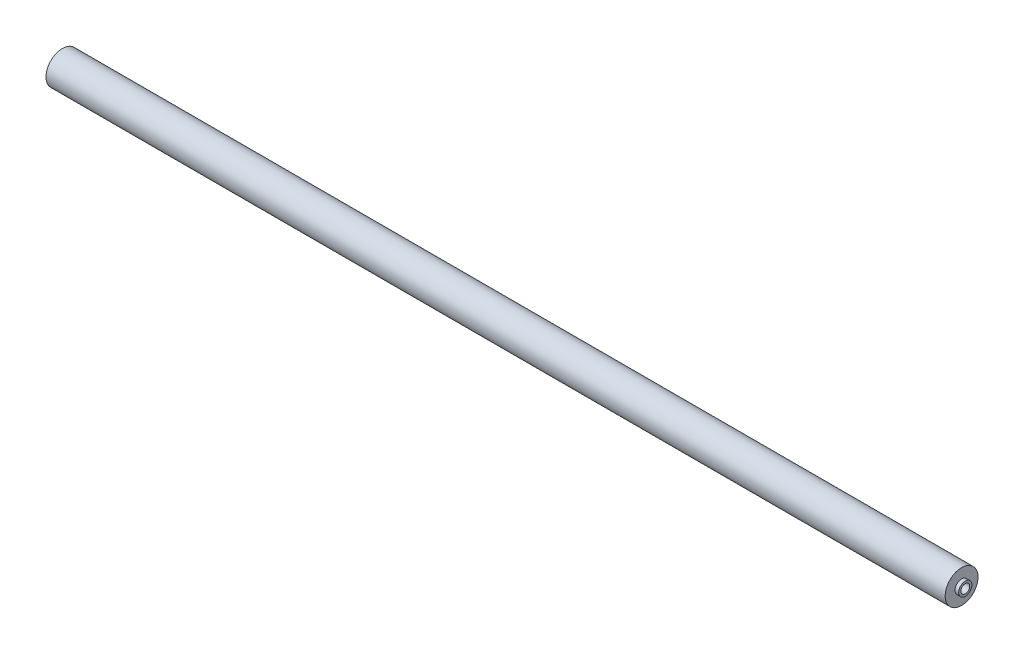
SolidWorks part; units mm, degrees
material "AISI Type A2 Tool Steel"
ref_plane "Front Plane" through (0, 0, 0) normal (0, 0, 1) x (1, 0, 0)
ref_plane "Top Plane" through (0, 0, 0) normal (0, 1, 0) x (1, 0, 0)
ref_plane "Right Plane" through (0, 0, 0) normal (1, 0, 0) x (0, 0, -1)
sketch "Sketch1" plane through (0, 0, 0) normal (0, 0, 1) x (1, 0, 0)
  line L0 (-669.4369, 125.3345) -> (0, 125.3345) construction
  line L2 (0, 125.3345) -> (0, 0) construction
  line L3 (-610.1, 147.2957) -> (-610.1, -13.5653) construction
  line L4 (-610.1, 134.8595) -> (-88.9, 134.8595)
  line L5 (-610.1, 134.8595) -> (-610.1, 129.8964)
  line L6 (-604.6353, 125.3345) -> (-93.3611, 125.3345)
  line L7 (-88.9, 134.8595) -> (-88.9, 129.1562)
  line L9 (-610.1, 129.8964) -> (-612.9579, 129.8964)
  line L10 (-612.9579, 129.8964) -> (-612.9579, 127.9082)
  line L11 (-612.9579, 127.9082) -> (-605.9011, 127.9082)
  line L12 (-605.9011, 127.9082) -> (-604.6353, 125.3345)
  line L14 (-88.9, 129.1562) -> (-86.7667, 129.1562)
  line L15 (-86.7667, 129.1562) -> (-86.7667, 127.9082)
  line L16 (-86.7667, 127.9082) -> (-91.5381, 127.9082)
  line L17 (-91.5381, 127.9082) -> (-93.3611, 125.3345)
  line L18 (-613.42, 125.3345) -> (-610.1, 125.3345) construction
  line L19 (-88.9, 147.2957) -> (-88.9, -13.5653) construction
  dimension "D1" = 19.05
revolve "Revolve1" add sketch "Sketch1" angle 360 about L0
